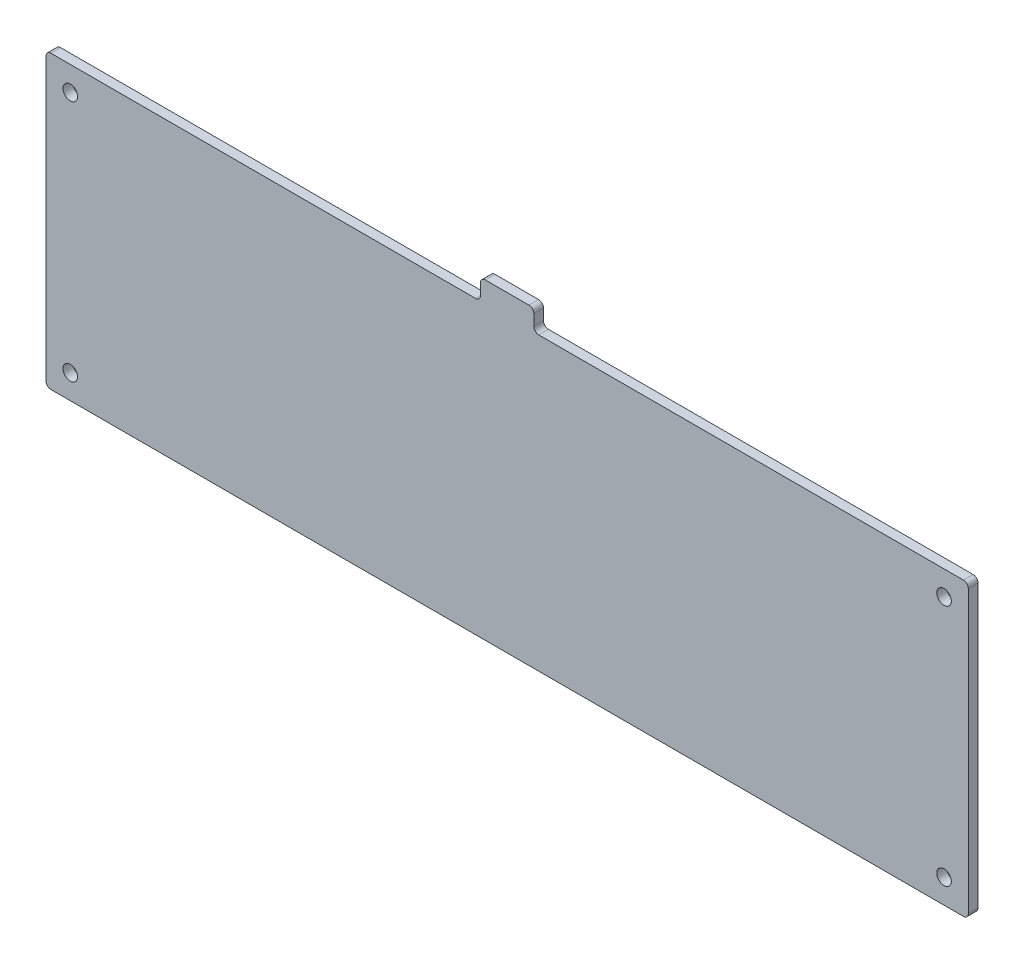
SolidWorks part; units mm, degrees
ref_plane "前视基准面" through (0, 0, 0) normal (0, 0, 1) x (1, 0, 0)
ref_plane "上视基准面" through (0, 0, 0) normal (0, 1, 0) x (1, 0, 0)
ref_plane "右视基准面" through (0, 0, 0) normal (1, 0, 0) x (0, 0, -1)
sketch "草图1" plane through (0, 0, 0) normal (0, 0, 1) x (1, 0, 0)
  line L0 (160, 46.5) -> (70.5, 46.5)
  line L1 (65, -13.5) -> (65, 93.6446) construction
  line L2 (-30, 46.5) -> (-30, -13.5)
  line L3 (-30, -13.5) -> (160, -13.5)
  line L4 (59.5, 46.5) -> (-30, 46.5)
  line L5 (160, 46.5) -> (160, -13.5)
  line L6 (59.5, 46.5) -> (59.5, 50.8)
  line L7 (59.5, 50.8) -> (70.5, 50.8)
  line L8 (70.5, 50.8) -> (70.5, 46.5)
  line L9 (-30, 16.5) -> (160, 16.5) construction
  circle A0 centre (-25, 41.5) radius 1.5
  circle A1 centre (155, 41.5) radius 1.5
  circle A2 centre (-25, -8.5) radius 1.5
  circle A3 centre (155, -8.5) radius 1.5
  dimension "D1" = 190
  dimension "D2" = 60
  dimension "D3" = 89.5
  dimension "D5" = 89.5
  dimension "D6" = 4.3
  dimension "D8" = 5
  dimension "D10" = 3
  dimension "D4" = 30
  dimension "D7" = 46.5
  dimension "D9" = 5
extrude "凸台-拉伸1" add sketch "草图1" along normal blind 2
fillet "圆角1" radius 1 8 edges at (-30, 46.5, 1) (-30, -13.5, 1) (160, -13.5, 1) (160, 46.5, 1) (70.5, 46.5, 1) (59.5, 46.5, 1) (70.5, 50.8, 1) (59.5, 50.8, 1)
